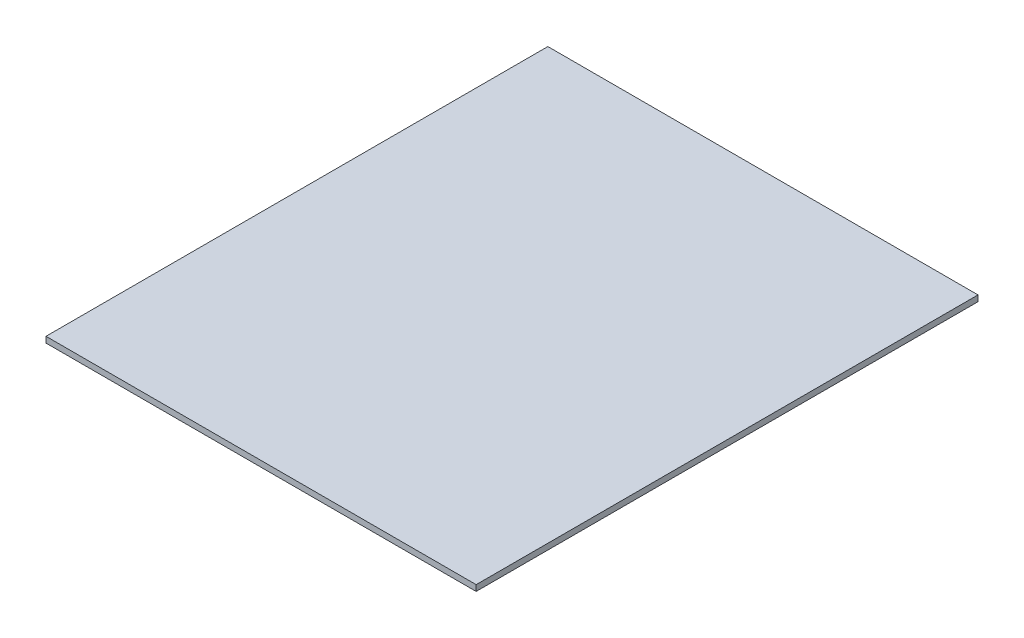
SolidWorks part; units mm, degrees
ref_plane "Front Plane" through (0, 0, 0) normal (0, 0, 1) x (1, 0, 0)
ref_plane "Top Plane" through (0, 0, 0) normal (0, 1, 0) x (1, 0, 0)
ref_plane "Right Plane" through (0, 0, 0) normal (1, 0, 0) x (0, 0, -1)
sketch "Sketch1" plane through (0, 0, 0) normal (0, 1, 0) x (1, 0, 0)
  line L1 (-60, -70) -> (60, -70)
  line L2 (-60, -70) -> (-60, 70)
  line L3 (-60, 70) -> (60, 70)
  line L4 (60, -70) -> (60, 70)
  line L5 (-60, -70) -> (60, 70) construction
  line L6 (-60, 70) -> (60, -70) construction
  point P0 (0, 0)
  dimension "D1" = 120
  dimension "D2" = 140
extrude "Boss-Extrude1" add sketch "Sketch1" along normal blind 1.65
